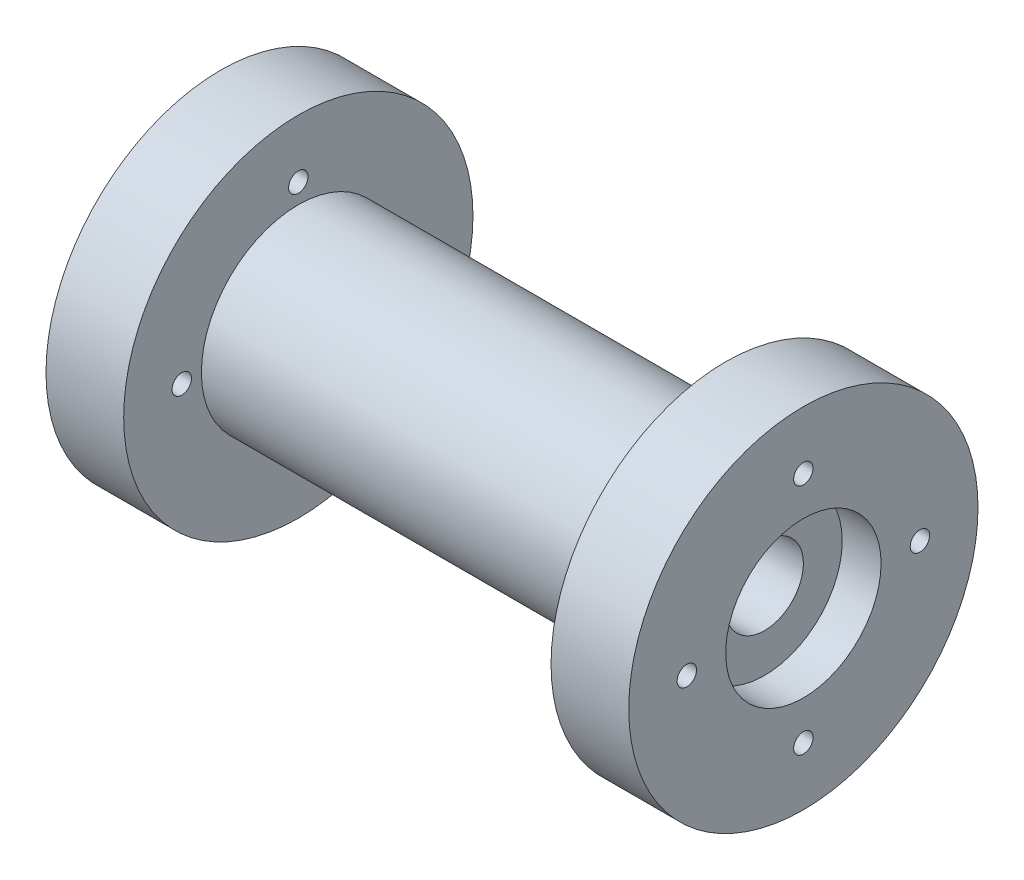
SolidWorks part; units mm, degrees
ref_plane "Front Plane" through (0, 0, 0) normal (0, 0, 1) x (1, 0, 0)
ref_plane "Top Plane" through (0, 0, 0) normal (0, 1, 0) x (1, 0, 0)
ref_plane "Right Plane" through (0, 0, 0) normal (1, 0, 0) x (0, 0, -1)
sketch "Sketch1" plane through (0, 0, 0) normal (0, 0, 1) x (1, 0, 0)
  line L0 (0, 0) -> (43.7895, 0) construction
  line L1 (0, 5) -> (0, 22.4737)
  line L2 (0, 22.4737) -> (10, 22.4737)
  line L3 (10, 22.4737) -> (10, 12.4737)
  line L4 (10, 12.4737) -> (65, 12.4737)
  line L5 (65, 12.4737) -> (65, 22.4737)
  line L6 (65, 22.4737) -> (75, 22.4737)
  line L7 (75, 22.4737) -> (75, 5)
  line L8 (75, 5) -> (0, 5)
  dimension "D1" = 5
  dimension "D2" = 75
  dimension "D3" = 10
  dimension "D4" = 10
revolve "Revolve1" add sketch "Sketch1" angle 360 about L0
sketch "Sketch2" plane through (0, 0, 0) normal (-1, 0, 0) x (0, 0, 1)
  line L0 (0, 0) -> (0, 15) construction
  circle A0 centre (0, 0) radius 15 construction
  circle A1 centre (0, 15) radius 1.25
  circle A2 centre (-15, 0) radius 1.25
  circle A3 centre (0, -15) radius 1.25
  circle A4 centre (15, 0) radius 1.25
  dimension "D1" = 30
  dimension "D2" = 2.5
extrude "Cut-Extrude1" cut sketch "Sketch2" against normal through all
sketch "Sketch3" plane through (0, 0, 0) normal (-1, 0, 0) x (0, 0, 1)
  circle A0 centre (0, 0) radius 10
  dimension "D1" = 20
extrude "Cut-Extrude2" cut sketch "Sketch3" against normal blind 5
sketch "Sketch4" plane through (75, 0, 0) normal (1, 0, 0) x (0, 0, -1)
  circle A0 centre (0, 0) radius 10
  dimension "D1" = 20
extrude "Cut-Extrude3" cut sketch "Sketch4" against normal blind 5
